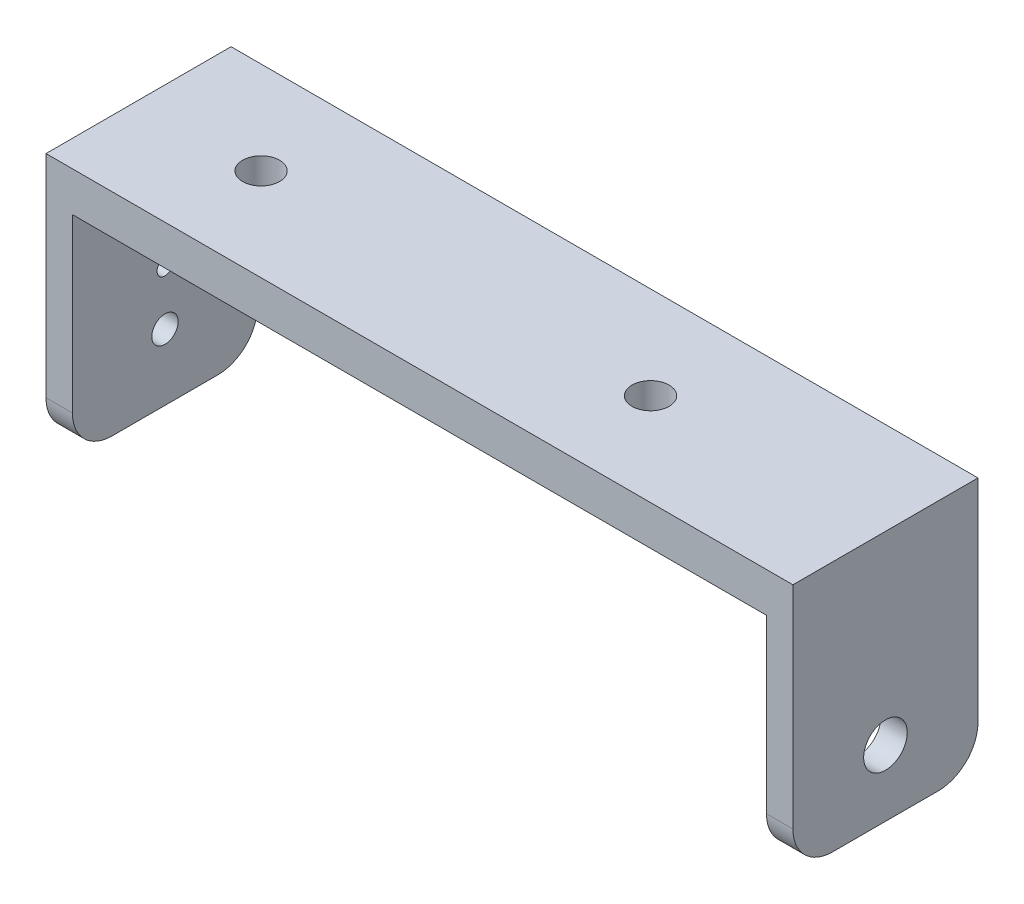
SolidWorks part; units mm, degrees
ref_plane "前视基准面" through (0, 0, 0) normal (0, 0, 1) x (1, 0, 0)
ref_plane "上视基准面" through (0, 0, 0) normal (0, 1, 0) x (1, 0, 0)
ref_plane "右视基准面" through (0, 0, 0) normal (1, 0, 0) x (0, 0, -1)
sketch "草图1" plane through (0, 0, 0) normal (0, 0, 1) x (1, 0, 0)
  line L0 (-28.25, 0) -> (-28.25, 19)
  line L1 (-28.25, 19) -> (28.25, 19)
  line L2 (28.25, 19) -> (28.25, 0)
  line L3 (28.25, 0) -> (26.25, 0)
  line L4 (26.25, 0) -> (26.25, 16)
  line L5 (26.25, 16) -> (-26.25, 16)
  line L6 (-26.25, 16) -> (-26.25, 0)
  line L7 (-26.25, 0) -> (-28.25, 0)
  line L8 (-61.4321, 26.241) -> (-59.0057, 26.241)
  line L9 (0, 0) -> (0, 21.894) construction
  dimension "D1" = 56.5
  dimension "D2" = 19
  dimension "D3" = 3
  dimension "D4" = 2
  dimension "D5" = 2
  dimension "D6" = 19
extrude "凸台-拉伸1" add sketch "草图1" along normal blind 14 contours L5 L9 L1 L0 L7 L6 | L9 L5 L4 L3 L2 L1
sketch "草图2" plane through (28.25, 0, 0) normal (1, 0, 0) x (0, 0, -1)
  line L0 (-7, 0) -> (-7, 19) construction
  line L1 (-14, 0) -> (0, 0) construction
  line L2 (-14, 19) -> (0, 19) construction
  circle A0 centre (-7, 5) radius 1.65
  dimension "D2" = 3.3
  dimension "D1" = 5
extrude "切除-拉伸1" cut sketch "草图2" against normal up to surface (2 mm away) up to face at (26.25, 8, 7)
sketch "草图3" plane through (0, 19, 0) normal (0, 1, 0) x (1, 0, 0)
  line L0 (-28.25, -7) -> (28.25, -7) construction
  line L1 (-28.25, -14) -> (-28.25, 0) construction
  line L2 (28.25, -14) -> (28.25, 0) construction
  line L3 (0, 0) -> (0, -14) construction
  line L4 (-28.25, 0) -> (28.25, 0) construction
  line L5 (-28.25, -14) -> (28.25, -14) construction
  line L6 (-4.25, 0) -> (-4.25, -14) construction
  circle A0 centre (-18.98, -7) radius 1.4
  circle A1 centre (10.48, -7) radius 1.4
  dimension "D2" = 2.8
  dimension "D1" = 29.46
  dimension "D3" = 4.25
extrude "切除-拉伸2" cut sketch "草图3" against normal blind 14
fillet "圆角1" radius 3 4 edges at (27.25, 0, 0) (27.25, 0, 14) (-27.25, 0, 0) (-27.25, 0, 14)
sketch "草图5" plane through (-28.25, 0, 0) normal (-1, 0, 0) x (0, 0, 1)
  line L0 (7, 5) -> (7, 20.3188) construction
  circle A0 centre (7, 5) radius 1.65 construction
  circle A1 centre (7, 5) radius 1.65 construction
  circle A2 centre (7, 9.085) radius 0.6
  circle A3 centre (7, 13.085) radius 0.6
  circle A4 centre (7, 5) radius 1
  dimension "D1" = 1.2
  dimension "D4" = 2
  dimension "D2" = 4.085
  dimension "D3" = 8.085
extrude "切除-拉伸3" cut sketch "草图5" against normal blind 10
